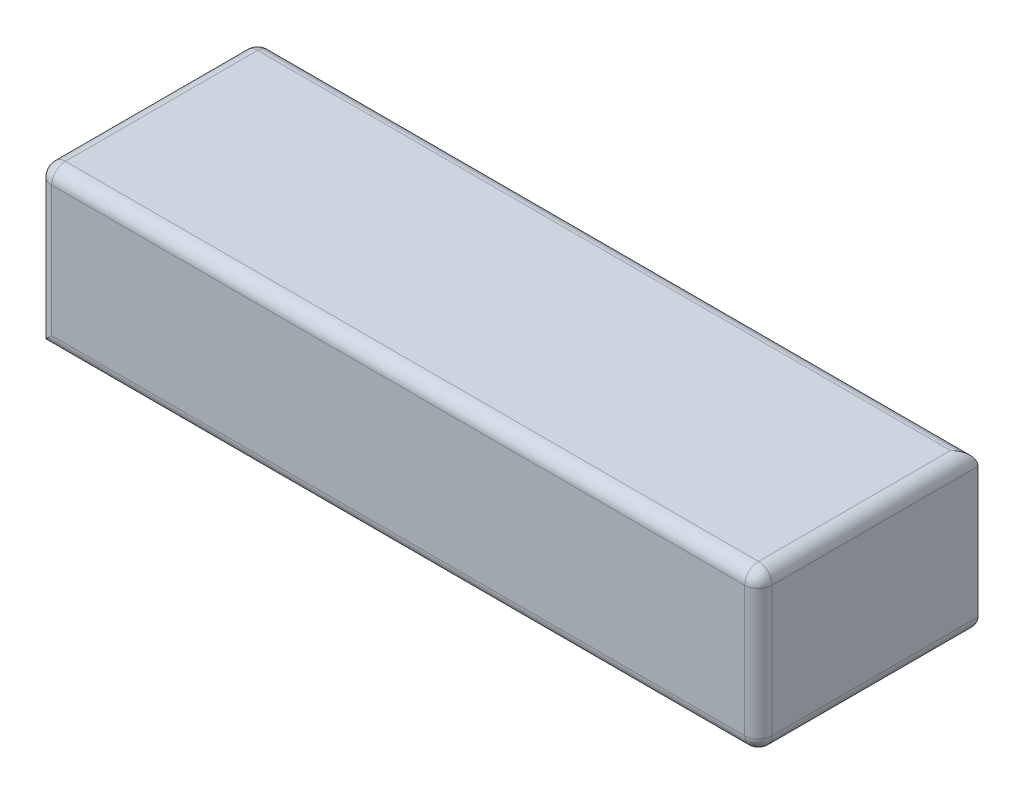
SolidWorks part; units mm, degrees
ref_plane "Front Plane" through (0, 0, 0) normal (0, 0, 1) x (1, 0, 0)
ref_plane "Top Plane" through (0, 0, 0) normal (0, 1, 0) x (1, 0, 0)
ref_plane "Right Plane" through (0, 0, 0) normal (1, 0, 0) x (0, 0, -1)
sketch "Sketch1" plane through (0, 0, 0) normal (0, 1, 0) x (1, 0, 0)
  line L1 (-52.5, -16) -> (52.5, -16)
  line L2 (-52.5, -16) -> (-52.5, 16)
  line L3 (-52.5, 16) -> (52.5, 16)
  line L4 (52.5, -16) -> (52.5, 16)
  line L5 (-52.5, -16) -> (52.5, 16) construction
  line L6 (-52.5, 16) -> (52.5, -16) construction
  point P0 (0, 0)
  dimension "D1" = 105
  dimension "D2" = 32
extrude "Boss-Extrude1" add sketch "Sketch1" along normal blind 23
fillet "Fillet1" radius 2 10 edges at (0, 23, 16) (-52.5, 23, 0) (0, 23, -16) (52.5, 23, 0) (-52.5, 11.5, -16) (-52.5, 11.5, 16) (0, 0, 16) (52.5, 11.5, 16) (0, 0, -16) (52.5, 0, 0)
